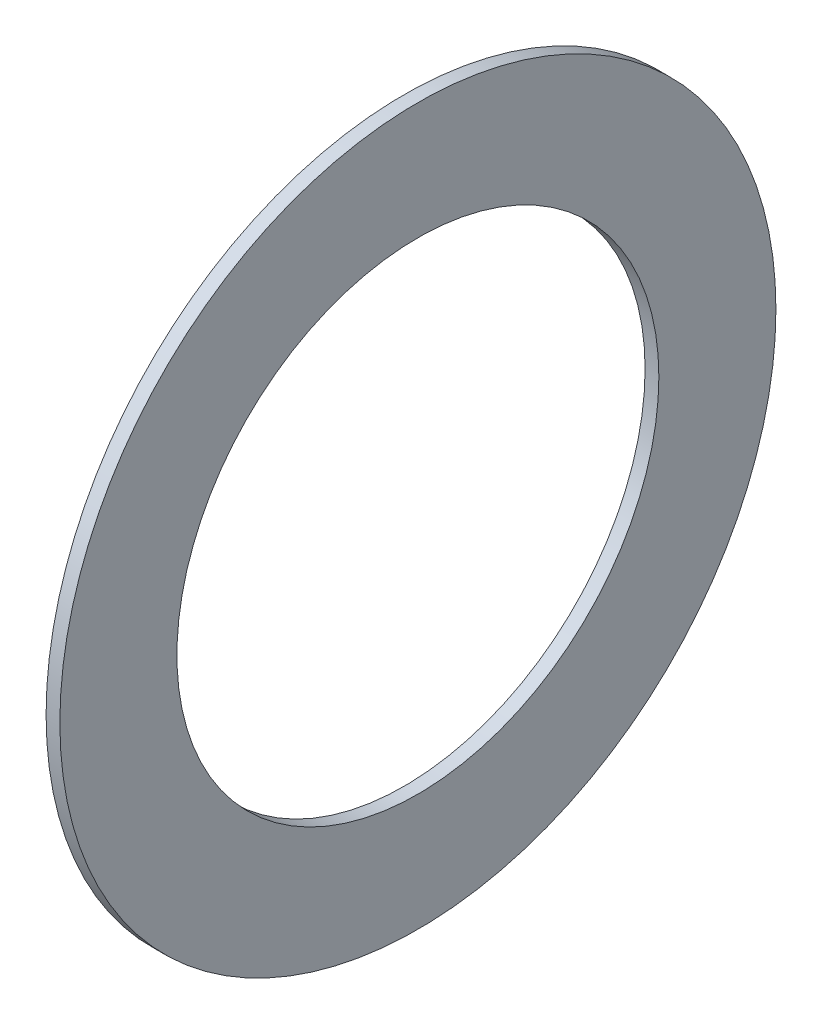
SolidWorks part; units mm, degrees
ref_plane "Front Plane" through (0, 0, 0) normal (0, 0, 1) x (1, 0, 0)
ref_plane "Top Plane" through (0, 0, 0) normal (0, 1, 0) x (1, 0, 0)
ref_plane "Right Plane" through (0, 0, 0) normal (1, 0, 0) x (0, 0, -1)
sketch "Sketch1" plane through (0, 0, 0) normal (1, 0, 0) x (0, 0, -1)
  circle A0 centre (0, 0) radius 26
  circle A1 centre (0, 0) radius 17.5
  dimension "OD" = 52
  dimension "Shaft Dia" = 35
extrude "Extrude1" add sketch "Sketch1" along normal blind 1
